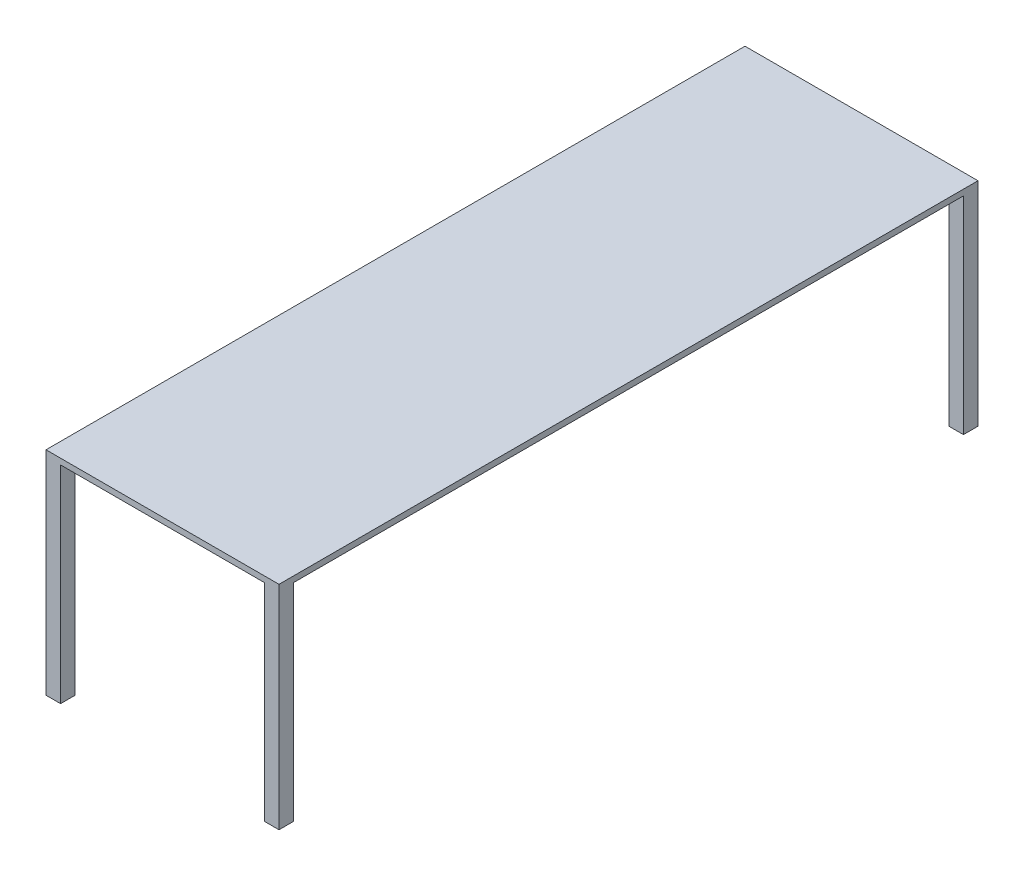
SolidWorks part; units mm, degrees
ref_plane "前视基准面" through (0, 0, 0) normal (0, 0, 1) x (1, 0, 0)
ref_plane "上视基准面" through (0, 0, 0) normal (0, 1, 0) x (1, 0, 0)
ref_plane "右视基准面" through (0, 0, 0) normal (1, 0, 0) x (0, 0, -1)
sketch "草图1" plane through (0, 0, 0) normal (0, 1, 0) x (1, 0, 0)
  line L1 (-400, -1200) -> (400, -1200)
  line L2 (-400, -1200) -> (-400, 1200)
  line L3 (-400, 1200) -> (400, 1200)
  line L4 (400, -1200) -> (400, 1200)
  line L5 (-400, -1200) -> (400, 1200) construction
  line L6 (-400, 1200) -> (400, -1200) construction
  point P0 (0, 0)
  dimension "D1" = 2400
  dimension "D2" = 800
extrude "凸台-拉伸1" add sketch "草图1" along normal blind 20
sketch "草图2" plane through (0, 0, 0) normal (0, -1, 0) x (-1, 0, 0)
  line L1 (-400, -1200) -> (-350, -1200)
  line L2 (-400, -1200) -> (-400, -1150)
  line L3 (-400, -1150) -> (-350, -1150)
  line L4 (-350, -1200) -> (-350, -1150)
  dimension "D1" = 50
  dimension "D2" = 50
extrude "凸台-拉伸2" add sketch "草图2" along normal blind 710
mirror "镜向1" about plane through (0, 0, 0) normal (0, 0, 1) of "凸台-拉伸2"
mirror "镜向2" about plane through (0, 0, 0) normal (1, 0, 0) of "镜向1", "凸台-拉伸2"
